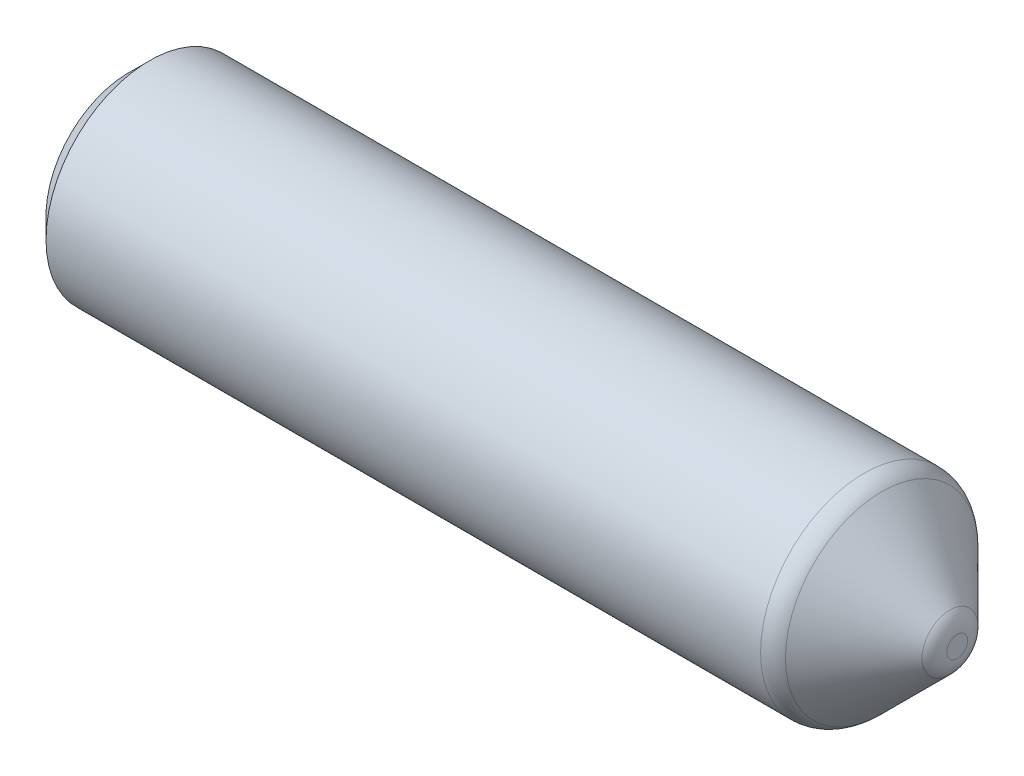
SolidWorks part; units mm, degrees
ref_plane "Front Plane" through (0, 0, 0) normal (0, 0, 1) x (1, 0, 0)
ref_plane "Top Plane" through (0, 0, 0) normal (0, 1, 0) x (1, 0, 0)
ref_plane "Right Plane" through (0, 0, 0) normal (1, 0, 0) x (0, 0, -1)
sketch "Sketch1" plane through (0, 0, 0) normal (1, 0, 0) x (0, 0, -1)
  circle A0 centre (0, 0) radius 50
  dimension "D1" = 100
extrude "Boss-Extrude1" add sketch "Sketch1" along normal mid plane 400
chamfer "Chamfer1" distance 40 angle 45 1 edges at (200, 0, -50)
fillet "Fillet1" radius 12 1 edges at (200, 0, -10)
fillet "Fillet2" radius 12 1 edges at (160, 0, -50)
chamfer "Chamfer2" distance 10 angle 45 1 edges at (-200, 0, -50)
